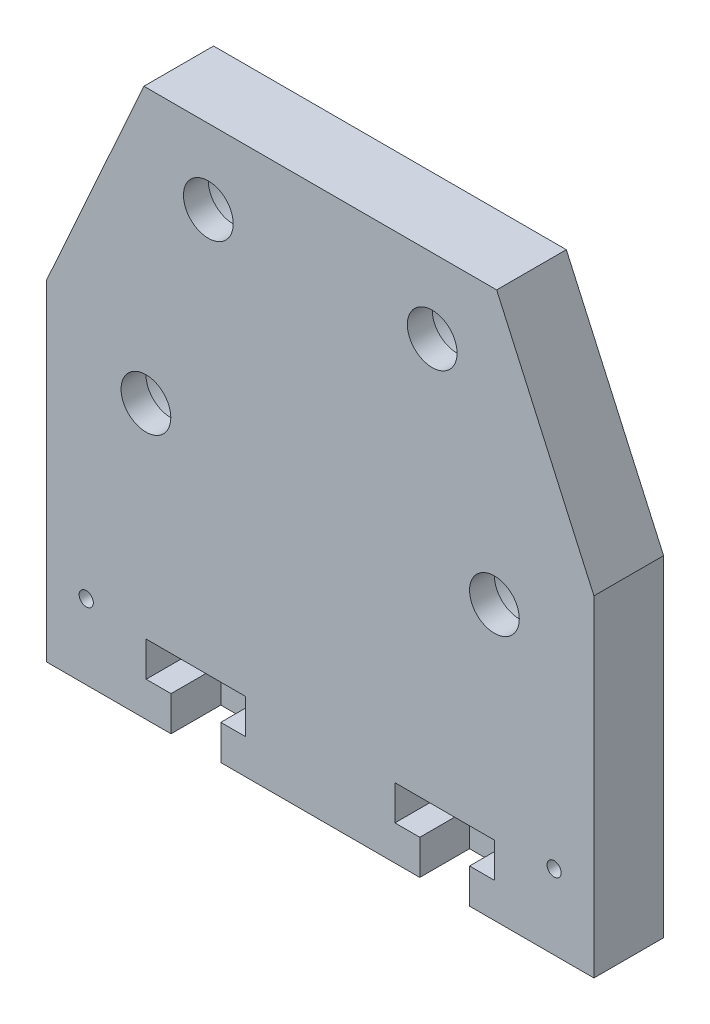
SolidWorks part; units mm, degrees
ref_plane "Front Plane" through (0, 0, 0) normal (0, 0, 1) x (1, 0, 0)
ref_plane "Top Plane" through (0, 0, 0) normal (0, 1, 0) x (1, 0, 0)
ref_plane "Right Plane" through (0, 0, 0) normal (1, 0, 0) x (0, 0, -1)
sketch "Sketch3" plane through (0, 0, 0) normal (0, 0, 1) x (1, 0, 0)
  line L0 (33.7824, 5.0217) -> (14.1872, -38.5696)
  line L1 (104.6814, 5.0217) -> (33.7824, 5.0217)
  line L3 (124.2289, -104.9783) -> (14.1872, -104.9783)
  line L5 (114.4868, -16.7913) -> (14.1872, -90.317) construction
  line L6 (124.2289, -90.3112) -> (23.977, -16.7913) construction
  line L7 (104.6814, 5.0217) -> (124.2289, -38.4636)
  line L8 (14.1872, -38.5696) -> (14.1872, -104.9783)
  line L9 (124.2289, -38.4636) -> (124.2289, -104.9783)
  circle A0 centre (91.7289, -9.9783) radius 11.05
  circle A1 centre (46.7289, -9.9783) radius 11.05
  circle A2 centre (104.2289, -49.9783) radius 11.05
  circle A3 centre (34.1872, -49.9783) radius 11.05
  point P0 (69.2229, -49.9725)
  dimension "D7" = 22.1
  dimension "D8" = 22.1
  dimension "D13" = 22.1
  dimension "D14" = 22.1
  dimension "D2" = 20
  dimension "D3" = 15
  dimension "D4" = 15
  dimension "D5" = 45
  dimension "D9" = 55
  dimension "D11" = 55
  dimension "D15" = 20
extrude "Boss-Extrude1" add sketch "Sketch3" along normal blind 14
sketch "Sketch4" plane through (0, 0, 14) normal (0, 0, 1) x (1, 0, 0)
  circle A0 centre (91.7289, -9.9783) radius 5
  circle A1 centre (46.7289, -9.9783) radius 5
  circle A2 centre (104.2289, -49.9783) radius 5
  circle A3 centre (34.1872, -49.9783) radius 5
  circle A4 centre (34.1872, -49.9783) radius 11.05 construction
  circle A5 centre (46.7289, -9.9783) radius 11.05 construction
  circle A6 centre (91.7289, -9.9783) radius 11.05 construction
  circle A7 centre (104.2289, -49.9783) radius 11.05 construction
  circle A8 centre (46.7289, -9.9783) radius 11.05
  circle A9 centre (91.7289, -9.9783) radius 11.05
  circle A10 centre (104.2289, -49.9783) radius 11.05
  circle A11 centre (34.1872, -49.9783) radius 11.05
  dimension "D6" = 22.1
  dimension "D8" = 22.1
  dimension "D10" = 22.1
  dimension "D12" = 22.1
  dimension "D13" = 10
  dimension "D14" = 10
  dimension "D15" = 10
  dimension "D16" = 10
  dimension "D1" = 0
  dimension "D2" = 0
  dimension "D3" = 0
  dimension "D4" = 0
  dimension "D5" = 0
  dimension "D7" = 0
  dimension "D9" = 0
  dimension "D11" = 0
sketch "Sketch5" plane through (0, 0, 14) normal (0, 0, 1) x (1, 0, 0)
  line L1 (39.2319, -97.9783) -> (49.2319, -97.9783)
  line L2 (39.2319, -97.9783) -> (39.2319, -104.9783)
  line L3 (39.2319, -104.9783) -> (49.2319, -104.9783)
  line L4 (49.2319, -97.9783) -> (49.2319, -104.9783)
  line L5 (34.2319, -90.9783) -> (54.2319, -90.9783)
  line L6 (34.2319, -90.9783) -> (34.2319, -97.9783)
  line L7 (34.2319, -97.9783) -> (54.2319, -97.9783)
  line L8 (54.2319, -90.9783) -> (54.2319, -97.9783)
  line L9 (89.2319, -97.9783) -> (99.2319, -97.9783)
  line L10 (89.2319, -97.9783) -> (89.2319, -104.9783)
  line L11 (89.2319, -104.9783) -> (99.2319, -104.9783)
  line L12 (99.2319, -97.9783) -> (99.2319, -104.9783)
  line L13 (84.2319, -90.9783) -> (104.2319, -90.9783)
  line L14 (84.2319, -90.9783) -> (84.2319, -97.9783)
  line L15 (84.2319, -97.9783) -> (104.2319, -97.9783)
  line L16 (104.2319, -90.9783) -> (104.2319, -97.9783)
  line L17 (14.1872, -104.9783) -> (124.2289, -104.9783) construction
  line M4 (14.1872, -104.9783) -> (124.2289, -104.9783)
  dimension "D3" = 0
  dimension "D4" = 7
  dimension "D5" = 0
  dimension "D6" = 7
  dimension "D7" = 20
  dimension "D8" = 0
  dimension "D9" = 7
  dimension "D10" = 0
  dimension "D11" = 7
  dimension "D14" = 10
  dimension "D15" = 20
  dimension "D16" = 10
extrude "Cut-Extrude3" cut sketch "Sketch5" against normal blind 10 contours L8 L5 L6 L7 L1 | L4 L1 L2 M4 | L16 L13 L14 L15 L9 | L12 L9 L10 M4
sketch "Sketch6" plane through (0, 0, 14) normal (0, 0, 1) x (1, 0, 0)
  circle A0 centre (46.7289, -9.9783) radius 11.05
  circle A1 centre (46.7289, -9.9783) radius 6
  circle A2 centre (91.7289, -9.9783) radius 11.05
  circle A3 centre (91.7289, -9.9783) radius 6
  circle A4 centre (34.1872, -49.9783) radius 11.05
  circle A5 centre (34.1872, -49.9783) radius 6
  circle A6 centre (104.2289, -49.9783) radius 11.05
  circle A7 centre (104.2289, -49.9783) radius 6
  circle A8 centre (46.7289, -9.9783) radius 11.05 construction
  circle A9 centre (91.7289, -9.9783) radius 11.05 construction
  circle A10 centre (34.1872, -49.9783) radius 11.05 construction
  circle A11 centre (104.2289, -49.9783) radius 11.05 construction
  dimension "D1" = 0
  dimension "D2" = 0
  dimension "D3" = 22.1
  dimension "D4" = 12
  dimension "D5" = 0
  dimension "D6" = 0
  dimension "D7" = 22.1
  dimension "D8" = 12
  dimension "D9" = 0
  dimension "D10" = 0
  dimension "D11" = 22.1
  dimension "D12" = 12
  dimension "D13" = 0
  dimension "D14" = 0
  dimension "D15" = 22.1
  dimension "D16" = 12
extrude "Boss-Extrude4" add sketch "Sketch6" against normal blind 5
sketch "Sketch7" plane through (0, 0, 14) normal (0, 0, 1) x (1, 0, 0)
  line L0 (14.1872, -104.9783) -> (39.2319, -104.9783) construction
  line L1 (14.1872, -38.5696) -> (14.1872, -104.9783) construction
  line L2 (99.2319, -104.9783) -> (124.2289, -104.9783) construction
  line L3 (124.2289, -104.9783) -> (124.2289, -38.4636) construction
  circle A0 centre (22.1872, -89.9783) radius 1.425
  circle A1 centre (116.2289, -89.9783) radius 1.425
  dimension "D1" = 2.85
  dimension "D6" = 2.85
  dimension "D2" = 15
  dimension "D3" = 8
  dimension "D4" = 15
  dimension "D5" = 8
sketch "Sketch8" plane through (0, 0, 14) normal (0, 0, 1) x (1, 0, 0)
  line L0 (14.1872, -104.9783) -> (39.2319, -104.9783) construction
  line L1 (99.2319, -104.9783) -> (124.2289, -104.9783) construction
  line L2 (124.2289, -104.9783) -> (124.2289, -38.4636) construction
  line L3 (14.1872, -38.5696) -> (14.1872, -104.9783) construction
  circle A0 centre (22.1872, -89.9783) radius 1.425
  circle A1 centre (116.2289, -89.9783) radius 1.425
  dimension "D5" = 2.85
  dimension "D6" = 2.85
  dimension "D1" = 15
  dimension "D2" = 15
  dimension "D3" = 8
  dimension "D4" = 8
extrude "Cut-Extrude5" cut sketch "Sketch8" against normal blind 14
extrude "Boss-Extrude2" add sketch "Sketch4" against normal blind 5
sketch "Sketch9" plane through (0, 0, 14) normal (0, 0, 1) x (1, 0, 0)
  text T0 "Phuoc Giau\r\nNgoc Quang"
